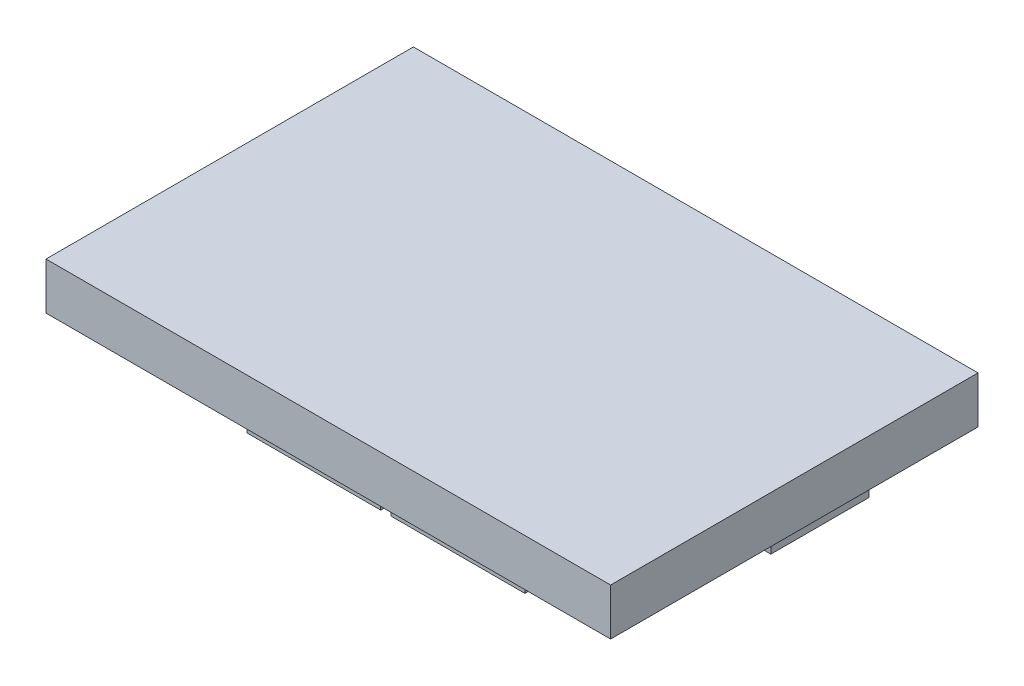
SolidWorks part; units mm, degrees
ref_plane "Front Plane" through (0, 0, 0) normal (0, 0, 1) x (1, 0, 0)
ref_plane "Top Plane" through (0, 0, 0) normal (0, 1, 0) x (1, 0, 0)
ref_plane "Right Plane" through (0, 0, 0) normal (1, 0, 0) x (0, 0, -1)
sketch "Sketch1" plane through (0, 0, 0) normal (0, 1, 0) x (1, 0, 0)
  line L1 (0, 0) -> (85.6, 0)
  line L2 (0, 0) -> (0, 55.7)
  line L3 (0, 55.7) -> (85.6, 55.7)
  line L4 (85.6, 0) -> (85.6, 55.7)
  line L5 (0, 0) -> (85.6, 55.7) construction
  line L6 (0, 55.7) -> (85.6, 0) construction
  point P4 (42.8, 27.85)
  dimension "D1" = 55.7
  dimension "D2" = 85.6
extrude "Boss-Extrude1" add sketch "Sketch1" along normal blind 7.1
sketch "Sketch2" plane through (0, 0, 0) normal (0, -1, 0) x (1, 0, 0)
  line L0 (0, 0) -> (85.6, 0) construction
  line L1 (28.45, -2) -> (48.75, -2)
  line L2 (28.45, -2) -> (28.45, -4.5)
  line L3 (28.45, -4.5) -> (48.75, -4.5)
  line L4 (48.75, -2) -> (48.75, -4.5)
  line L5 (28.45, -2) -> (48.75, -4.5) construction
  line L6 (28.45, -4.5) -> (48.75, -2) construction
  line L7 (50.3, -2) -> (70.6, -2)
  line L8 (50.3, -2) -> (50.3, -4.5)
  line L9 (50.3, -4.5) -> (70.6, -4.5)
  line L10 (70.6, -2) -> (70.6, -4.5)
  line L11 (50.3, -2) -> (70.6, -4.5) construction
  line L12 (50.3, -4.5) -> (70.6, -2) construction
  line L13 (61.6, -53.2) -> (46.3, -53.2)
  line L14 (61.6, -53.2) -> (61.6, -50.7)
  line L15 (61.6, -50.7) -> (46.3, -50.7)
  line L16 (46.3, -53.2) -> (46.3, -50.7)
  line L17 (61.6, -53.2) -> (46.3, -50.7) construction
  line L18 (61.6, -50.7) -> (46.3, -53.2) construction
  line L19 (43.75, -53.2) -> (28.45, -53.2)
  line L20 (43.75, -53.2) -> (43.75, -50.7)
  line L21 (43.75, -50.7) -> (28.45, -50.7)
  line L22 (28.45, -53.2) -> (28.45, -50.7)
  line L23 (43.75, -53.2) -> (28.45, -50.7) construction
  line L24 (43.75, -50.7) -> (28.45, -53.2) construction
  line L25 (85.6, -55.7) -> (0, -55.7) construction
  line L26 (85.6, 0) -> (85.6, -55.7) construction
  point P4 (38.6, -3.25)
  point P9 (60.45, -3.25)
  point P14 (53.95, -51.95)
  point P19 (36.1, -51.95)
  dimension "D1" = 2.5
  dimension "D2" = 20.3
  dimension "D3" = 20.3
  dimension "D4" = 15.3
  dimension "D5" = 15.3
  dimension "D6" = 1.55
  dimension "D7" = 2.55
  dimension "D8" = 2
  dimension "D9" = 2.5
  dimension "D10" = 24
  dimension "D11" = 15
extrude "Boss-Extrude2" add sketch "Sketch2" along normal blind 2.5
sketch "Sketch3" plane through (0, 0, 0) normal (0, -1, 0) x (1, 0, 0)
  line L0 (85.6, 0) -> (85.6, -55.7) construction
  line L1 (84.6, -25.3) -> (69.6, -25.3)
  line L2 (84.6, -25.3) -> (84.6, -40.2)
  line L3 (84.6, -40.2) -> (69.6, -40.2)
  line L4 (69.6, -25.3) -> (69.6, -40.2)
  line L5 (84.6, -25.3) -> (69.6, -40.2) construction
  line L6 (84.6, -40.2) -> (69.6, -25.3) construction
  line L7 (85.6, -55.7) -> (0, -55.7) construction
  point P4 (77.1, -32.75)
  dimension "D1" = 14.9
  dimension "D2" = 15
  dimension "D3" = 1
  dimension "D4" = 15.5
extrude "Boss-Extrude3" add sketch "Sketch3" along normal blind 2
